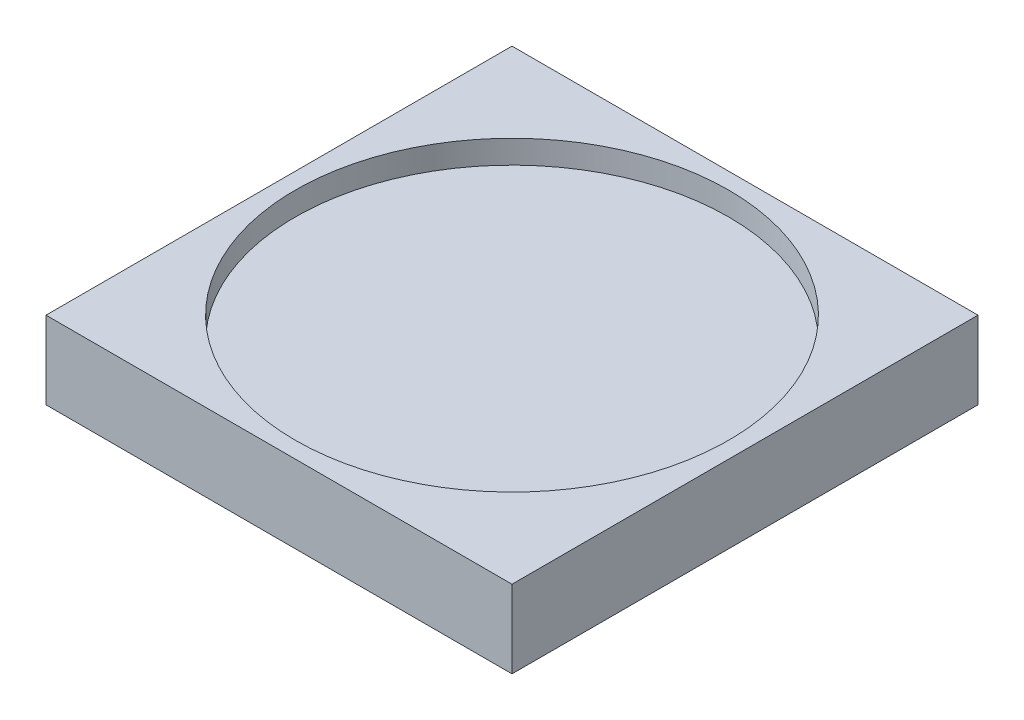
SolidWorks part; units mm, degrees
ref_plane "Front Plane" through (0, 0, 0) normal (0, 0, 1) x (1, 0, 0)
ref_plane "Top Plane" through (0, 0, 0) normal (0, 1, 0) x (1, 0, 0)
ref_plane "Right Plane" through (0, 0, 0) normal (1, 0, 0) x (0, 0, -1)
sketch "Sketch1" plane through (0, 0, 0) normal (0, 1, 0) x (1, 0, 0)
  line L1 (-15, -15) -> (15, -15)
  line L2 (-15, -15) -> (-15, 15)
  line L3 (-15, 15) -> (15, 15)
  line L4 (15, -15) -> (15, 15)
  line L5 (-15, -15) -> (15, 15) construction
  line L6 (-15, 15) -> (15, -15) construction
  point P0 (0, 0)
  dimension "D1" = 30
  dimension "D2" = 30
extrude "Boss-Extrude1" add sketch "Sketch1" along normal blind 5
sketch "Sketch2" plane through (0, 5, 0) normal (0, 1, 0) x (1, 0, 0)
  circle A0 centre (0, 0) radius 13.95
  dimension "D1" = 27.9
extrude "Cut-Extrude1" cut sketch "Sketch2" against normal blind 1.5
